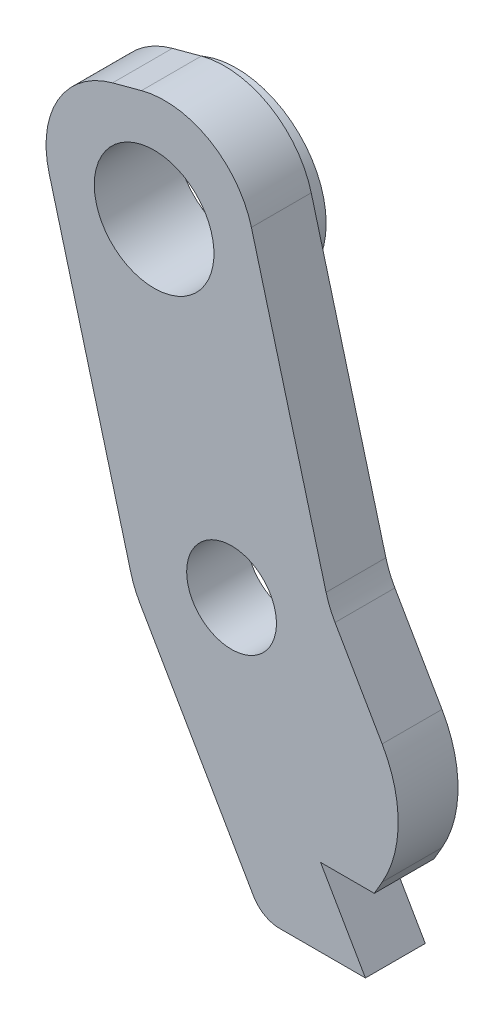
SolidWorks part; units mm, degrees
ref_plane "前视基准面" through (0, 0, 0) normal (0, 0, 1) x (1, 0, 0)
ref_plane "上视基准面" through (0, 0, 0) normal (0, 1, 0) x (1, 0, 0)
ref_plane "右视基准面" through (0, 0, 0) normal (1, 0, 0) x (0, 0, -1)
sketch "草图1" plane through (0, 0, -37.2525) normal (0, 0, 1) x (1, 0, 0)
  line L0 (-5.7048, 8.9994) -> (-14.0004, 8.9994) construction
  line L1 (-14.0004, 8.9994) -> (-11.3913, 4.4807) construction
  line L2 (-14.0004, 8.9994) -> (-17.4945, 22.0394) construction
  line L3 (-10.7389, 10.3504) -> (-14.1137, 22.9452)
  line L5 (-14.1137, 22.9452) -> (-20.8752, 21.1335)
  line L6 (-17.2619, 7.6483) -> (-12.976, 0.2258)
  line L7 (-20.8752, 21.1335) -> (-17.2619, 7.6483)
  line L11 (-12.976, 0.2258) -> (-9.5249, 0.2258)
  line L13 (-9.5249, 0.2258) -> (-11.025, 2.8238)
  line L14 (-11.025, 2.8238) -> (-9.2297, 2.8239)
  line L18 (-10.7389, 10.3504) -> (-7.8115, 5.2805)
  line L19 (-7.8115, 5.2805) -> (-9.2297, 2.8239)
  circle A0 centre (-16.5886, 18.6586) radius 2
  circle A1 centre (-14.0004, 8.9994) radius 1.5
  point P1 (-20.9819, 21.0724)
  dimension "D7" = 120
  dimension "D4" = 7
  dimension "D9" = 3.5
  dimension "D10" = 3.5
  dimension "D3" = 3
  dimension "D8" = 10
  dimension "D1" = 4
  dimension "D2" = 59.997
  dimension "D5" = 7
  dimension "D6" = 3
  dimension "D11" = 105
extrude "凸台-拉伸1" add sketch "草图1" along normal up to surface (2 mm away)
fillet "圆角1" radius 3 4 edges at (-14.1127, 22.9459, -36.2525) (-20.8743, 21.1344, -36.2525) (-10.7385, 10.3509, -36.2525) (-17.2615, 7.6491, -36.2525)
fillet "圆角2" radius 4 1 edges at (-7.8113, 5.2809, -36.2525)
fillet "圆角3" radius 1 1 edges at (-12.976, 0.2264, -36.2525)
sketch "草图2" plane through (-0.251, -0.0681, -37.2525) normal (0, 0, 1) x (1, 0, 0)
  circle A0 centre (-16.3367, 18.7274) radius 3
  circle A1 centre (-16.3367, 18.7274) radius 2 construction
  circle A3 centre (-16.3367, 18.7274) radius 2
  dimension "D1" = 6
extrude "凸台-拉伸2" add sketch "草图2" against normal blind 0.75
